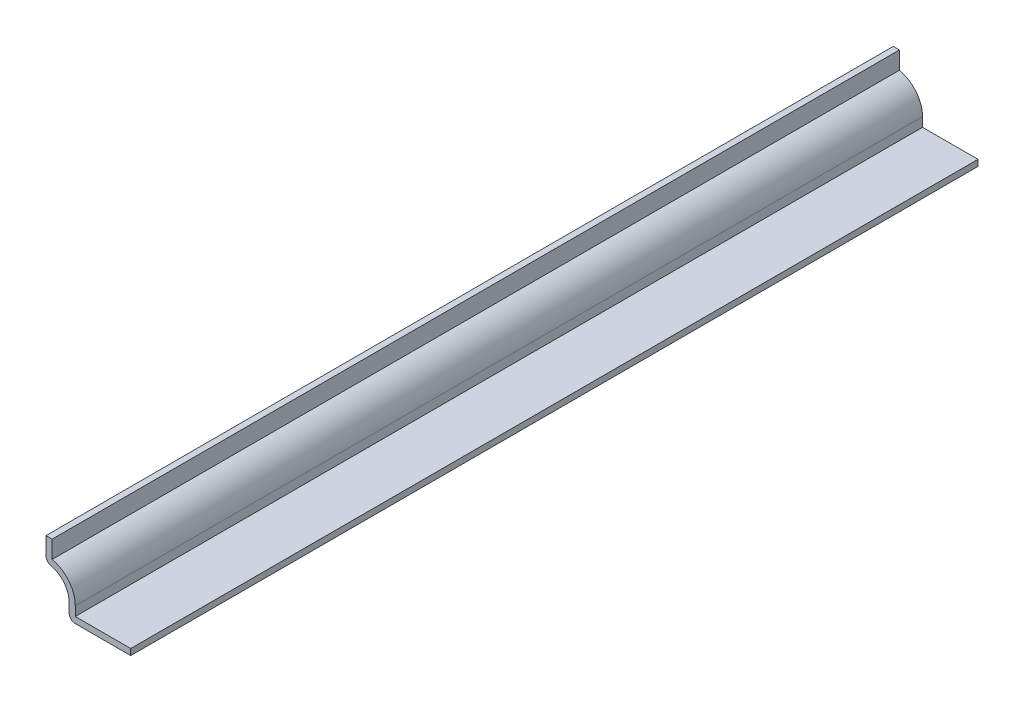
SolidWorks part; units mm, degrees
ref_plane "Front Plane" through (0, 0, 0) normal (0, 0, 1) x (1, 0, 0)
ref_plane "Top Plane" through (0, 0, 0) normal (0, 1, 0) x (1, 0, 0)
ref_plane "Right Plane" through (0, 0, 0) normal (1, 0, 0) x (0, 0, -1)
sketch "Sketch1" plane through (0, 0, 0) normal (0, 0, 1) x (1, 0, 0)
  line L0 (0, 0) -> (-12.7, 0)
  line L1 (-12.7, 0) -> (-12.7, 3.175)
  line L2 (-17.4625, 7.9375) -> (-17.4625, 12.7)
  arc A0 (-12.7, 3.175) -> (-17.4625, 7.9375) centre (-17.4625, 3.175) ccw
  point P6 (0, 0)
  dimension "D1" = 17.4625
  dimension "D2" = 12.7
  dimension "D3" = 4.7625
  dimension "D4" = 4.7625
extrude "Extrude-Thin1" add sketch "Sketch1" against normal blind 174.625 thin
fillet "Fillet1" radius 1.27 2 edges at (-12.7, 0, -87.3125) (-17.4625, 7.9375, -87.3125)
